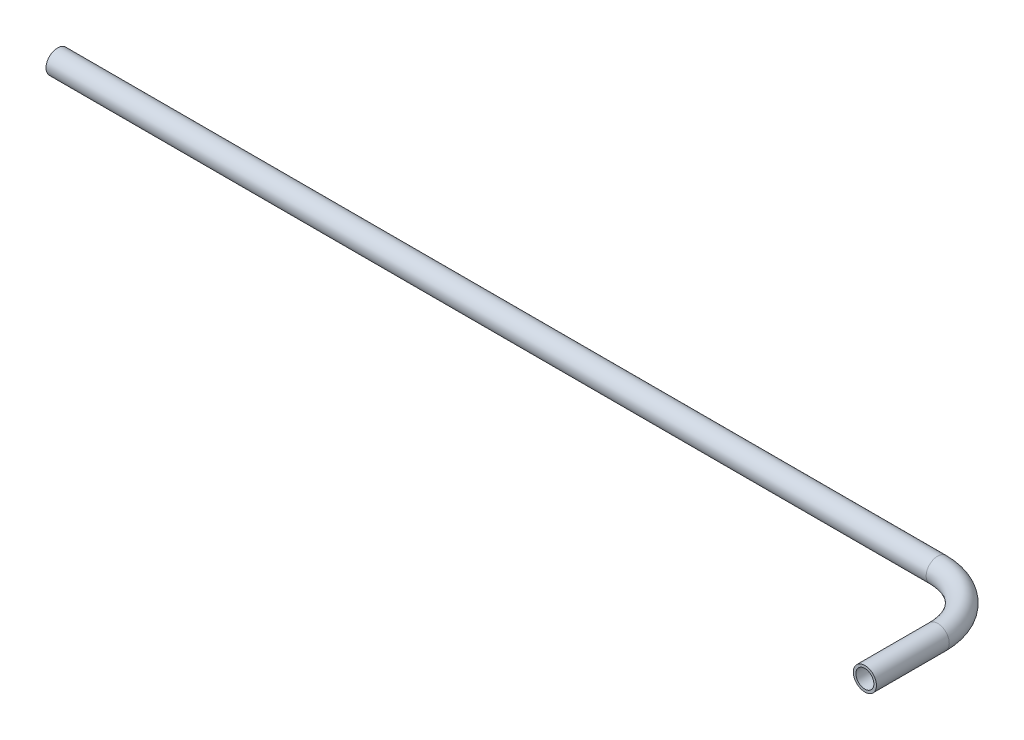
SolidWorks part; units mm, degrees
material "AISI 304"
ref_plane "Front Plane" through (0, 0, 0) normal (0, 0, 1) x (1, 0, 0)
ref_plane "Top Plane" through (0, 0, 0) normal (0, 1, 0) x (1, 0, 0)
ref_plane "Right Plane" through (0, 0, 0) normal (1, 0, 0) x (0, 0, -1)
sketch "Sketch1" plane through (0, 0, 0) normal (0, 1, 0) x (1, 0, 0)
  line L1 (-257.7, 36) -> (-16, 36)
  line L2 (0, 20) -> (0, 0)
  arc A0 (-16, 36) -> (0, 20) centre (-16, 20) cw
  point P0 (-145.2285, 52.346)
  dimension "D1" = 16
  dimension "D2" = 257.7
  dimension "D4" = 20
sketch "Sketch2" plane through (0, 0, 0) normal (0, 0, 1) x (1, 0, 0)
  circle A0 centre (0, 0) radius 3.175
  dimension "D1" = 6.35
sweep "Sweep-Thin1" add profiles "Sketch2" path "Sketch1" parameters "D1"=0.7112
